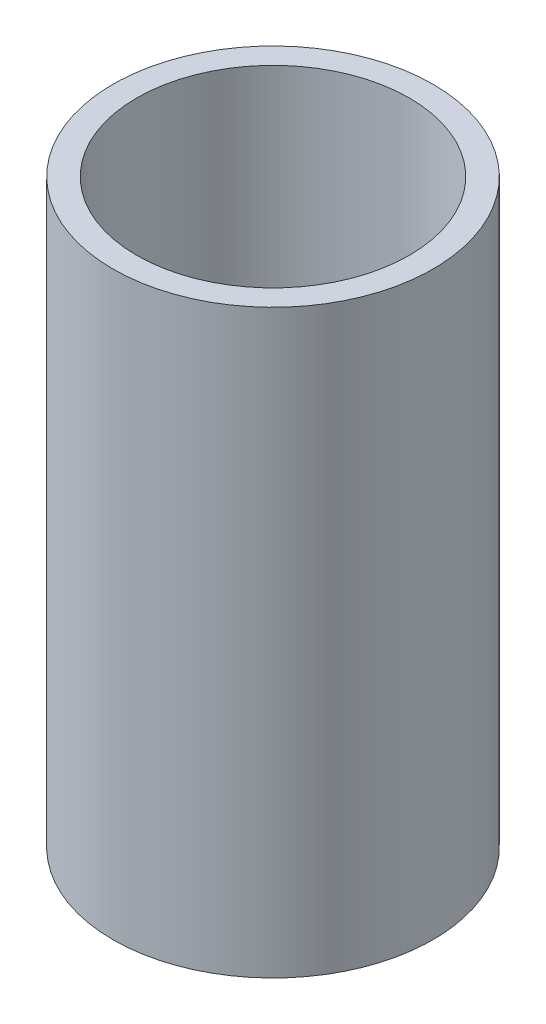
SolidWorks part; units mm, degrees
ref_plane "Front Plane" through (0, 0, 0) normal (0, 0, 1) x (1, 0, 0)
ref_plane "Top Plane" through (0, 0, 0) normal (0, 1, 0) x (1, 0, 0)
ref_plane "Right Plane" through (0, 0, 0) normal (1, 0, 0) x (0, 0, -1)
sketch "Sketch1" plane through (0, 0, 0) normal (0, 1, 0) x (1, 0, 0)
  circle A0 centre (0, 0) radius 13.5
  circle A1 centre (0, 0) radius 11.5
extrude "Boss-Extrude1" add sketch "Sketch1" along normal blind 49
